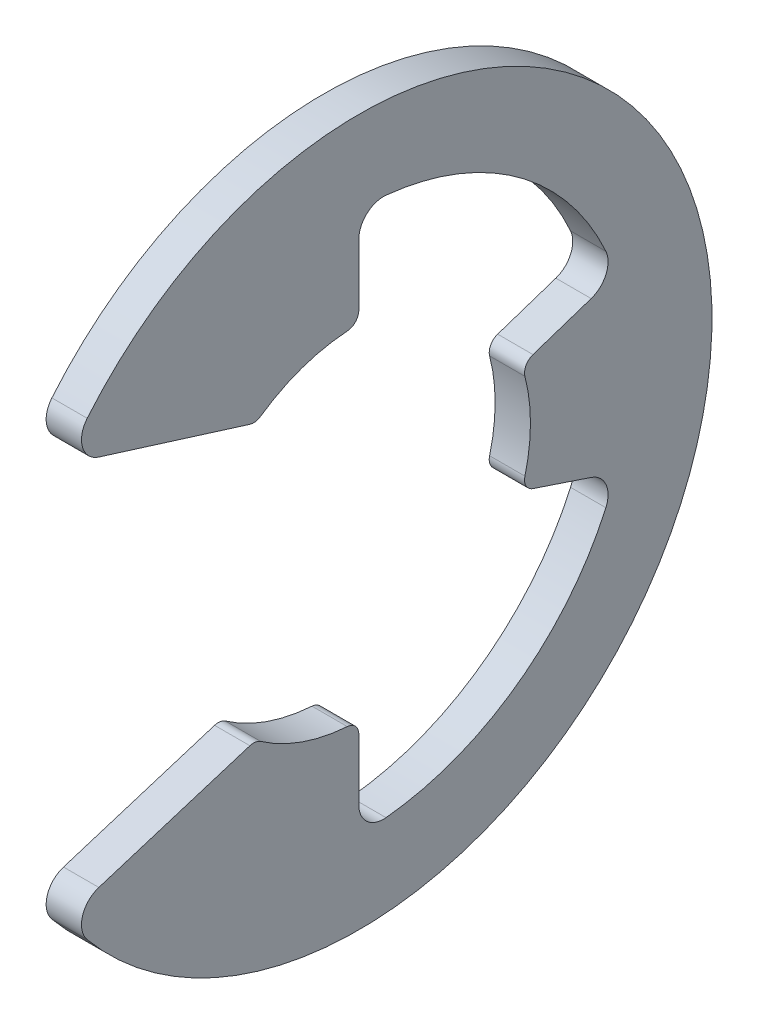
SolidWorks part; units mm, degrees
ref_plane "Front" through (0, 0, 0) normal (0, 0, 1) x (1, 0, 0)
ref_plane "Top" through (0, 0, 0) normal (0, 1, 0) x (1, 0, 0)
ref_plane "Right" through (0, 0, 0) normal (1, 0, 0) x (0, 0, -1)
sketch "Sketch1" plane through (0, 0, 0) normal (1, 0, 0) x (0, 0, -1)
  line L0 (-5.2732, -3.5377) -> (-1.8517, -2.4689)
  line L1 (-5.2732, 3.5377) -> (-1.8517, 2.4689)
  line L2 (0, -3.0861) -> (0, -4.8702)
  line L3 (0, 3.0861) -> (0, 4.8702)
  line L4 (2.9277, -0.9759) -> (4.6203, -1.5401)
  line L5 (2.9277, 0.9759) -> (4.6203, 1.5401)
  line L6 (0, 0) -> (-3.0861, 0) construction
  line L7 (2.9277, 0.9759) -> (2.9277, -0.9759) construction
  line L8 (0, -3.0861) -> (-1.8517, -2.4689) construction
  line L9 (0, 6.35) -> (0, -6.35) construction
  circle A2 centre (0, 0) radius 3.0861 construction
  arc A3 (-5.2732, -3.5377) -> (-5.2732, 3.5377) centre (0, 0) ccw
  arc A4 (-1.8517, -2.4689) -> (0, -3.0861) centre (0, 0) ccw
  arc A5 (-1.8517, 2.4689) -> (0, 3.0861) centre (0, 0) cw
  arc A6 (2.9277, 0.9759) -> (2.9277, -0.9759) centre (0, 0) cw
  arc A7 (0, -4.8702) -> (4.6203, -1.5401) centre (0, 0) ccw
  arc A8 (4.6203, 1.5401) -> (0, 4.8702) centre (0, 0) ccw
  point P8 (0, 3.0861)
  point P12 (0, 6.35)
  dimension "Free Diameter" = 6.1722
  dimension "D1" = 4.8702
  dimension "Ring OD" = 12.7
  dimension "D2" = 3.6089
  dimension "D10" = 4.9378
sketch "Sketch4" plane through (0, 0, 0) normal (0, 0, 1) x (1, 0, 0)
  line L0 (-0.3175, 6.35) -> (0.3175, 6.35) construction
  point P3 (0, 6.35)
  dimension "Ring Thickness" = 0.635
sketch "Sketch3" plane through (0, 0, 0) normal (1, 0, 0) x (0, 0, -1)
  line L6 (2.9277, -0.9759) -> (4.6203, -1.5401)
  line L7 (0, -4.8702) -> (0, -3.0861)
  line L8 (-1.8517, -2.4689) -> (-5.2732, -3.5377)
  line L9 (-5.2732, 3.5377) -> (-1.8517, 2.4689)
  line L10 (0, 3.0861) -> (0, 4.8702)
  line L11 (4.6203, 1.5401) -> (2.9277, 0.9759)
  line L12 (2.9277, -0.9759) -> (4.6203, -1.5401)
  line L13 (0, -4.8702) -> (0, -3.0861)
  line L14 (-1.8517, -2.4689) -> (-5.2732, -3.5377)
  line L15 (-5.2732, 3.5377) -> (-1.8517, 2.4689)
  line L16 (0, 3.0861) -> (0, 4.8702)
  line L17 (4.6203, 1.5401) -> (2.9277, 0.9759)
  arc A6 (0, -4.8702) -> (4.6203, -1.5401) centre (0, 0) ccw
  arc A7 (-1.8517, -2.4689) -> (0, -3.0861) centre (0, 0) ccw
  arc A8 (-5.2732, -3.5377) -> (-5.2732, 3.5377) centre (0, 0) ccw
  arc A9 (0, 3.0861) -> (-1.8517, 2.4689) centre (0, 0) ccw
  arc A10 (4.6203, 1.5401) -> (0, 4.8702) centre (0, 0) ccw
  arc A11 (2.9277, -0.9759) -> (2.9277, 0.9759) centre (0, 0) ccw
  arc A12 (0, -4.8702) -> (4.6203, -1.5401) centre (0, 0) ccw
  arc A13 (-1.8517, -2.4689) -> (0, -3.0861) centre (0, 0) ccw
  arc A14 (-5.2732, -3.5377) -> (-5.2732, 3.5377) centre (0, 0) ccw
  arc A15 (0, 3.0861) -> (-1.8517, 2.4689) centre (0, 0) ccw
  arc A16 (4.6203, 1.5401) -> (0, 4.8702) centre (0, 0) ccw
  arc A17 (2.9277, -0.9759) -> (2.9277, 0.9759) centre (0, 0) ccw
  dimension "D1" = 0
extrude "Boss-Extrude1" add sketch "Sketch3" along normal up to vertex (0.3175 mm away) and the other way up to vertex (0.3175 mm away) up to point (0.3175, 6.35, 0) other way up to point (-0.3175, 6.35, 0)
fillet "Fillet1" radius 0.4445 6 edges at (0, -4.8702, 0) (0, -1.5401, -4.6203) (0, 1.5401, -4.6203) (0, 4.8702, 0) (0, -3.5377, 5.2732) (0, 3.5377, 5.2732)
fillet "Fillet2" radius 0.2223 6 edges at (0, -3.0861, 0) (0, -2.4689, 1.8517) (0, 0.9759, -2.9277) (0, -0.9759, -2.9277) (0, 2.4689, 1.8517) (0, 3.0861, 0)
equation "\"D1@Sketch1\" =  ( \"Ring OD@Sketch1\" + \"Free Diameter@Sketch1\" )  / 3.875"
equation "\"D10@Sketch1\"=\"Free Diameter@Sketch1\" * .8"
equation "\"D1@Fillet1\"=\"Ring Thickness@Sketch4\"*.7"
equation "\"D1@Fillet2\"=\"D1@Fillet1\"/2"
